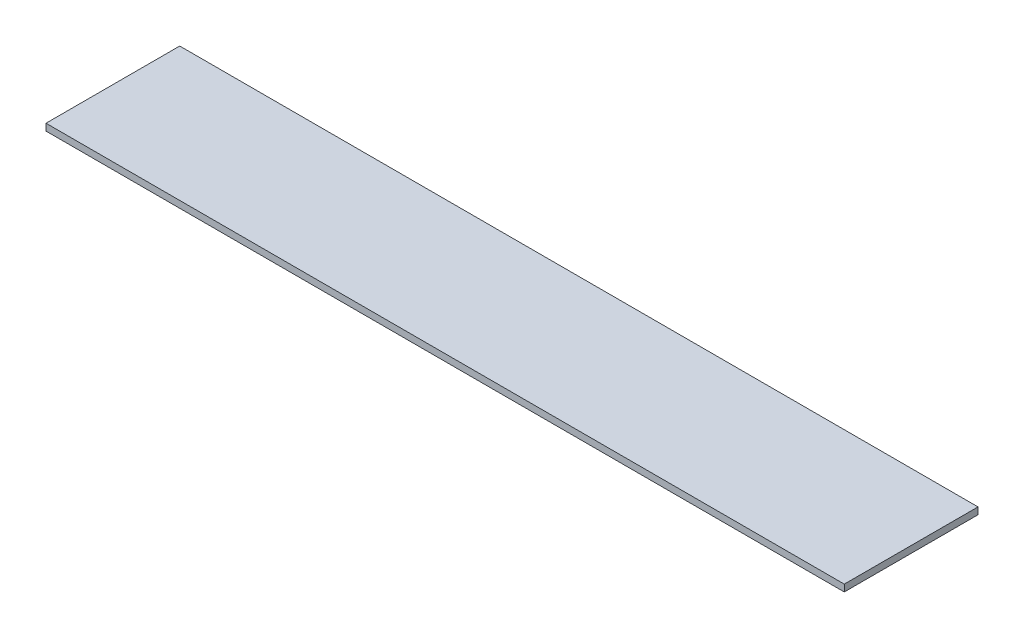
SolidWorks part; units mm, degrees
ref_plane "Front Plane" through (0, 0, 0) normal (0, 0, 1) x (1, 0, 0)
ref_plane "Top Plane" through (0, 0, 0) normal (0, 1, 0) x (1, 0, 0)
ref_plane "Right Plane" through (0, 0, 0) normal (1, 0, 0) x (0, 0, -1)
sketch "Sketch1" plane through (0, 0, 0) normal (0, 1, 0) x (1, 0, 0)
  line L1 (-895.7174, 410.3533) -> (772.1701, 410.3533)
  line L2 (-895.7174, 410.3533) -> (-895.7174, 130.9533)
  line L3 (-895.7174, 130.9533) -> (772.1701, 130.9533)
  line L4 (772.1701, 410.3533) -> (772.1701, 130.9533)
  dimension "D1" = 1667.8875
  dimension "D2" = 279.4
extrude "Boss-Extrude1" add sketch "Sketch1" along normal blind 14.2875
